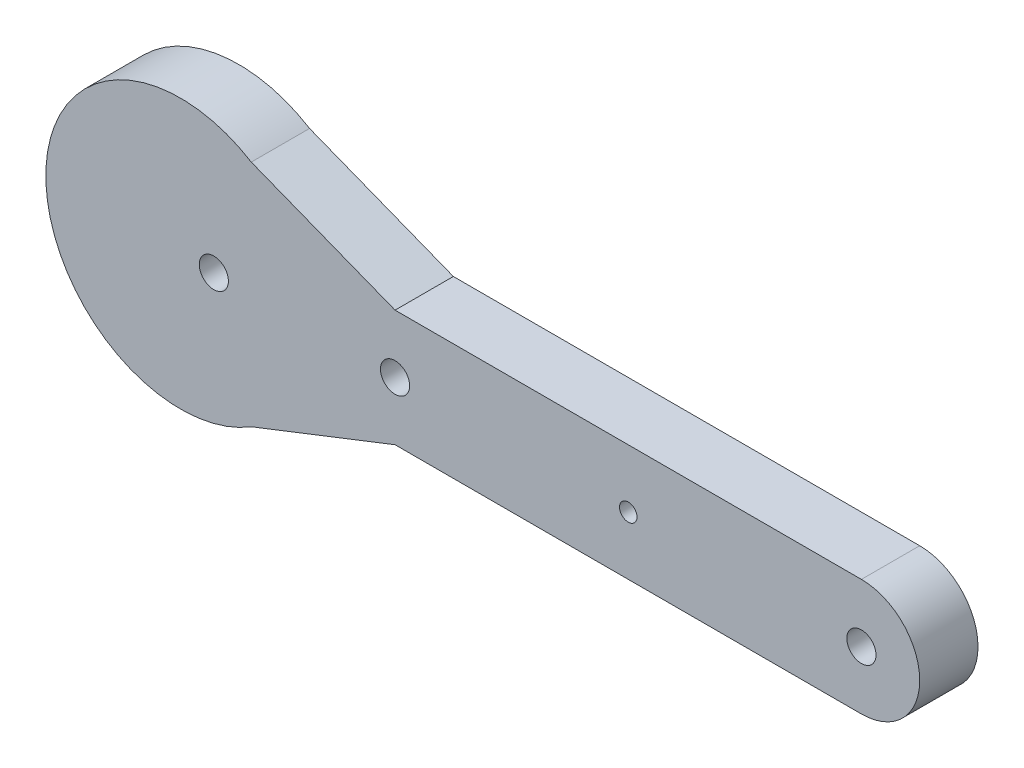
SolidWorks part; units mm, degrees
ref_plane "Plan de face" through (0, 0, 0) normal (0, 0, 1) x (1, 0, 0)
ref_plane "Plan de dessus" through (0, 0, 0) normal (0, 1, 0) x (1, 0, 0)
ref_plane "Plan de droite" through (0, 0, 0) normal (1, 0, 0) x (0, 0, -1)
sketch "Esquisse1" plane through (0, 0, 0) normal (0, 0, 1) x (1, 0, 0)
  line L0 (0, 10) -> (-36.8078, 10) construction
  line L1 (0, 0) -> (80, 0)
  line L3 (0, 20) -> (80, 20)
  line L5 (0, 20) -> (-24.6673, 29.6584)
  line L6 (0, 0) -> (-24.6673, -9.6584)
  arc A1 (80, 20) -> (80, 0) centre (80, 10) cw
  circle A2 centre (0, 10) radius 2.5
  circle A3 centre (80, 10) radius 2.5
  arc A7 (-24.6673, 29.6584) -> (-24.6673, -9.6584) centre (-36.8078, 10) ccw
  circle A8 centre (-31.0911, 10) radius 2.5
  circle A9 centre (40, 10) radius 1.5
  point P14 (-59.9129, 10)
  dimension "D1" = 5
  dimension "D2" = 5
  dimension "D6" = 5
  dimension "D7" = 23.1051
  dimension "D10" = 3
  dimension "D3" = 20
  dimension "D4" = 80
  dimension "D5" = 36.8078
  dimension "D8" = 59.9129
  dimension "D9" = 31.0911
  dimension "D11" = 40
extrude "Boss.-Extru.1" add sketch "Esquisse1" along normal blind 10
